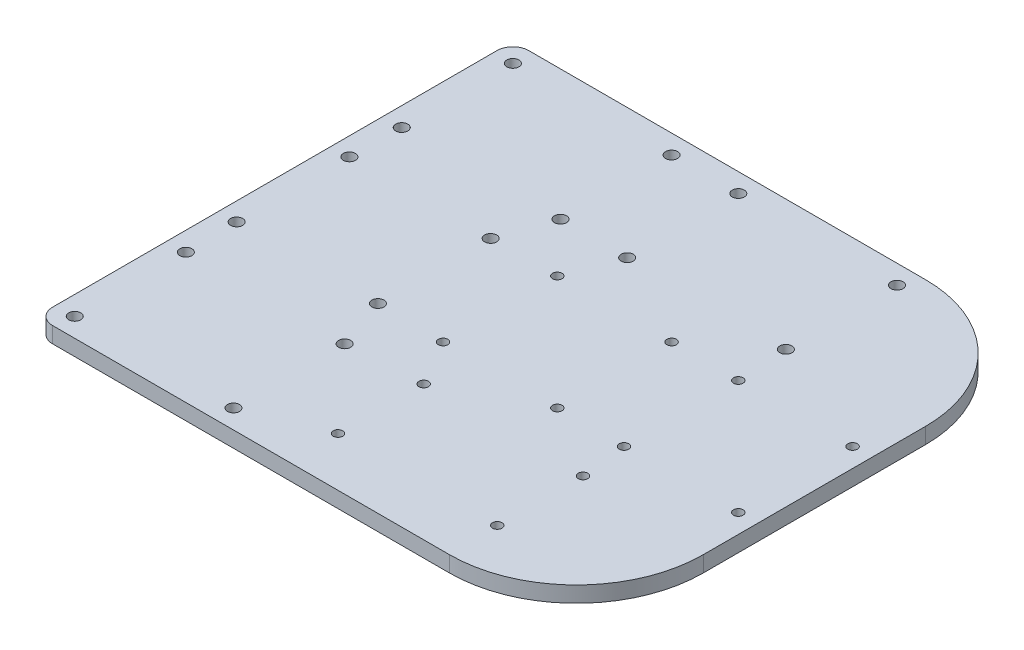
SolidWorks part; units mm, degrees
ref_plane "前视基准面" through (0, 0, 0) normal (0, 0, 1) x (1, 0, 0)
ref_plane "上视基准面" through (0, 0, 0) normal (0, 1, 0) x (1, 0, 0)
ref_plane "右视基准面" through (0, 0, 0) normal (1, 0, 0) x (0, 0, -1)
sketch "草图1" plane through (0, 0, 0) normal (0, 1, 0) x (1, 0, 0)
  line L1 (-21, 21) -> (21, 21) construction
  line L2 (-21, 21) -> (-21, -21) construction
  line L3 (-21, -21) -> (21, -21) construction
  line L4 (21, 21) -> (21, -21) construction
  line L5 (0, -21) -> (0, 21) construction
  line L6 (-21, 0) -> (21, 0) construction
  line L7 (-61, 21) -> (-61, -21) construction
  line L8 (-107.7243, 0) -> (136.5568, 0) construction
  line L9 (-30, 72) -> (-30, 31) construction
  line L14 (-15, -31) -> (46, -31) construction
  line L15 (-15, -31) -> (-15, -61) construction
  line L16 (-36, 21) -> (-36, -21) construction
  line L17 (-30, 72) -> (-86, 72) construction
  line L18 (-30, 72) -> (-30, 31) construction
  line L19 (-30, 31) -> (-86, 31) construction
  line L20 (-86, 72) -> (-86, 31) construction
  line L21 (-30, -31) -> (-86, -31) construction
  line L22 (-36, 21) -> (-86, 21) construction
  line L23 (-36, 21) -> (-36, -21) construction
  line L24 (-36, -21) -> (-86, -21) construction
  line L25 (-86, 21) -> (-86, -21) construction
  line L26 (-30, -72) -> (-30, -31) construction
  line L27 (-86, -72) -> (-86, -31) construction
  line L28 (-30, -72) -> (-86, -72) construction
  line L29 (-15, -61) -> (46, -61) construction
  line L30 (46, -31) -> (46, -61) construction
  line L31 (-15, -31) -> (46, -31) construction
  line L35 (36, 21) -> (78, 21) construction
  line L36 (36, 21) -> (36, -21) construction
  line L37 (36, -21) -> (78, -21) construction
  line L38 (78, 21) -> (78, -21) construction
  line L39 (57, -21) -> (57, 21) construction
  line L40 (36, 0) -> (78, 0) construction
  line L41 (-15, 72) -> (41, 72) construction
  line L42 (-15, 72) -> (-15, 31) construction
  line L43 (-15, 31) -> (41, 31) construction
  line L44 (41, 72) -> (41, 31) construction
  line L45 (-18, 18) -> (18, 18) construction
  line L46 (-18, 18) -> (-18, -18) construction
  line L47 (-18, -18) -> (18, -18) construction
  line L48 (18, 18) -> (18, -18) construction
  line L49 (0, -18) -> (0, 18) construction
  line L50 (-18, 0) -> (18, 0) construction
  line L51 (39, 18) -> (75, 18) construction
  line L52 (39, 18) -> (39, -18) construction
  line L53 (39, -18) -> (75, -18) construction
  line L54 (75, 18) -> (75, -18) construction
  line L55 (57, -18) -> (57, 18) construction
  line L56 (39, 0) -> (75, 0) construction
  line L57 (-83.25, 21) -> (-83.25, -21) construction
  line L58 (-107.7243, 17.75) -> (136.5568, 17.75) construction
  line L59 (15.5, -31) -> (15.5, -61) construction
  line L60 (-15, -46) -> (46, -46) construction
  line L61 (-9.58, -31) -> (-9.58, -61) construction
  line L62 (-15, -59.5) -> (46, -59.5) construction
  line L63 (-86, 51.5) -> (-30, 51.5) construction
  line L64 (-86, 34) -> (-30, 34) construction
  line L65 (-58, 72) -> (-58, 31) construction
  line L66 (-83, 72) -> (-83, 31) construction
  line L67 (-22.5, 72) -> (-22.5, 31) construction
  line L69 (-89, 75) -> (81, 75)
  line L70 (-89, 75) -> (-89, -75)
  line L71 (-89, -75) -> (81, -75)
  line L72 (81, 75) -> (81, -75)
  circle A0 centre (75, 18) radius 1.5
  circle A1 centre (18, 18) radius 1.5
  circle A2 centre (-83.25, 17.75) radius 1.9
  circle A3 centre (-9.58, -59.5) radius 1.5
  circle A4 centre (-83, 34) radius 1.9
  circle A5 centre (-83, 69) radius 1.9
  circle A6 centre (-33, 34) radius 1.9
  circle A7 centre (-33, 69) radius 1.9
  circle A8 centre (-12, 34) radius 1.9
  circle A9 centre (-12, 69) radius 1.9
  circle A10 centre (38, 69) radius 1.9
  circle A11 centre (38, 34) radius 1.9
  circle A12 centre (-38.75, 17.75) radius 1.9
  circle A13 centre (-18, 18) radius 1.5
  circle A14 centre (39, 18) radius 1.5
  circle A15 centre (75, -18) radius 1.5
  circle A16 centre (39, -18) radius 1.5
  circle A17 centre (18, -18) radius 1.5
  circle A18 centre (-18, -18) radius 1.5
  circle A19 centre (-83, -69) radius 1.9
  circle A20 centre (-33, -69) radius 1.9
  circle A21 centre (-33, -34) radius 1.9
  circle A22 centre (-83, -34) radius 1.9
  circle A23 centre (-38.75, -17.75) radius 1.9
  circle A24 centre (-83.25, -17.75) radius 1.9
  circle A25 centre (40.58, -59.5) radius 1.5
  circle A26 centre (40.58, -32.5) radius 1.5
  circle A27 centre (-9.58, -32.5) radius 1.5
  point P0 (0, 0)
  point P7 (0, 0)
  point P36 (57, 0)
  point P41 (57, 0)
  dimension "D26" = 3
  dimension "D27" = 3
  dimension "D30" = 3.8
  dimension "D33" = 3
  dimension "D36" = 3.8
  dimension "D1" = 42
  dimension "D2" = 42
  dimension "D4" = 41
  dimension "D5" = 0
  dimension "D3" = 10
  dimension "D7" = 56
  dimension "D9" = 50
  dimension "D11" = 15
  dimension "D12" = 10
  dimension "D13" = 42
  dimension "D14" = 42
  dimension "D15" = 15
  dimension "D16" = 144
  dimension "D17" = 164
  dimension "D6" = 61
  dimension "D10" = 30
  dimension "D18" = 41
  dimension "D19" = 56
  dimension "D20" = 15
  dimension "D21" = 10
  dimension "D22" = 36
  dimension "D23" = 36
  dimension "D24" = 36
  dimension "D25" = 36
  dimension "D38" = 3
  dimension "D39" = 3
  dimension "D40" = 3
  dimension "D41" = 3
  dimension "D8" = 15
  dimension "D28" = 22.25
  dimension "D29" = 17.75
  dimension "D31" = 25.08
  dimension "D32" = 13.5
  dimension "D34" = 17.5
  dimension "D35" = 25
  dimension "D37" = 7.5
extrude "凸台-拉伸1" add sketch "草图1" along normal blind 5
fillet "圆角1" radius 5 2 edges at (-89, 2.5, 75) (-89, 2.5, -75)
fillet "圆角2" radius 40 2 edges at (81, 2.5, -75) (81, 2.5, 75)
